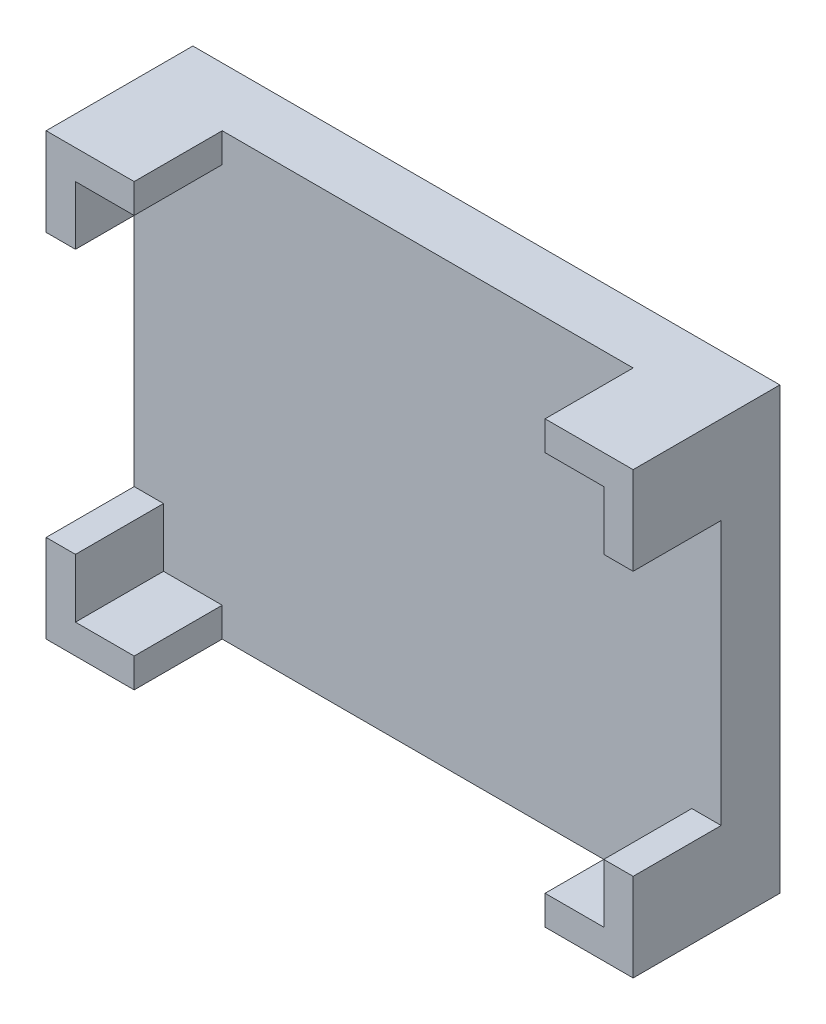
SolidWorks part; units mm, degrees
ref_plane "Front Plane" through (0, 0, 0) normal (0, 0, 1) x (1, 0, 0)
ref_plane "Top Plane" through (0, 0, 0) normal (0, 1, 0) x (1, 0, 0)
ref_plane "Right Plane" through (0, 0, 0) normal (1, 0, 0) x (0, 0, -1)
sketch "Sketch1" plane through (0, 0, 0) normal (0, 0, 1) x (1, 0, 0)
  line L1 (0, 0) -> (20, 0)
  line L2 (0, 0) -> (0, 15)
  line L3 (0, 15) -> (20, 15)
  line L4 (20, 0) -> (20, 15)
  dimension "D1" = 20
  dimension "D2" = 15
extrude "Boss-Extrude2" add sketch "Sketch1" along normal blind 2
sketch "Sketch2" plane through (0, 0, 2) normal (0, 0, 1) x (1, 0, 0)
  line L1 (0, 15) -> (1, 15)
  line L2 (0, 15) -> (0, 12)
  line L3 (0, 12) -> (1, 12)
  line L4 (1, 14) -> (1, 12)
  line L5 (0, 15) -> (3, 15)
  line L6 (0, 15) -> (0, 14)
  line L7 (1, 14) -> (3, 14)
  line L8 (3, 15) -> (3, 14)
  line L9 (0, 0) -> (1, 0)
  line L10 (0, 0) -> (0, 3)
  line L11 (0, 3) -> (1, 3)
  line L12 (1, 1) -> (1, 3)
  line L13 (0, 0) -> (3, 0)
  line L14 (0, 0) -> (0, 1)
  line L15 (1, 1) -> (3, 1)
  line L16 (3, 0) -> (3, 1)
  line L17 (20, 0) -> (19, 0)
  line L18 (20, 0) -> (20, 3)
  line L19 (20, 3) -> (19, 3)
  line L20 (19, 1) -> (19, 3)
  line L21 (20, 0) -> (17, 0)
  line L22 (20, 0) -> (20, 1)
  line L23 (19, 1) -> (17, 1)
  line L24 (17, 0) -> (17, 1)
  line L25 (20, 15) -> (17, 15)
  line L26 (20, 15) -> (20, 14)
  line L27 (19, 14) -> (17, 14)
  line L28 (17, 15) -> (17, 14)
  line L29 (20, 15) -> (19, 15)
  line L30 (20, 15) -> (20, 12)
  line L31 (20, 12) -> (19, 12)
  line L32 (19, 14) -> (19, 12)
  line M16 (0, 15) -> (0, 0)
  line M17 (0, 0) -> (20, 0)
  line M18 (20, 0) -> (20, 15)
  line M19 (20, 15) -> (0, 15)
  dimension "D1" = 1
  dimension "D2" = 3
  dimension "D3" = 1
  dimension "D4" = 3
  dimension "D5" = 1
  dimension "D6" = 3
  dimension "D7" = 3
  dimension "D8" = 1
  dimension "D9" = 1
  dimension "D10" = 1
  dimension "D11" = 3
  dimension "D12" = 3
  dimension "D13" = 1
  dimension "D14" = 1
  dimension "D15" = 3
extrude "Boss-Extrude3" add sketch "Sketch2" along normal blind 3 contours L8 L2 L3 L4 L7 M19 M16 | L16 L15 L12 L11 L10 M17 M16 | L27 L32 L31 L25 L28 M18 M19 | L21 L24 L23 L20 L19 L18
